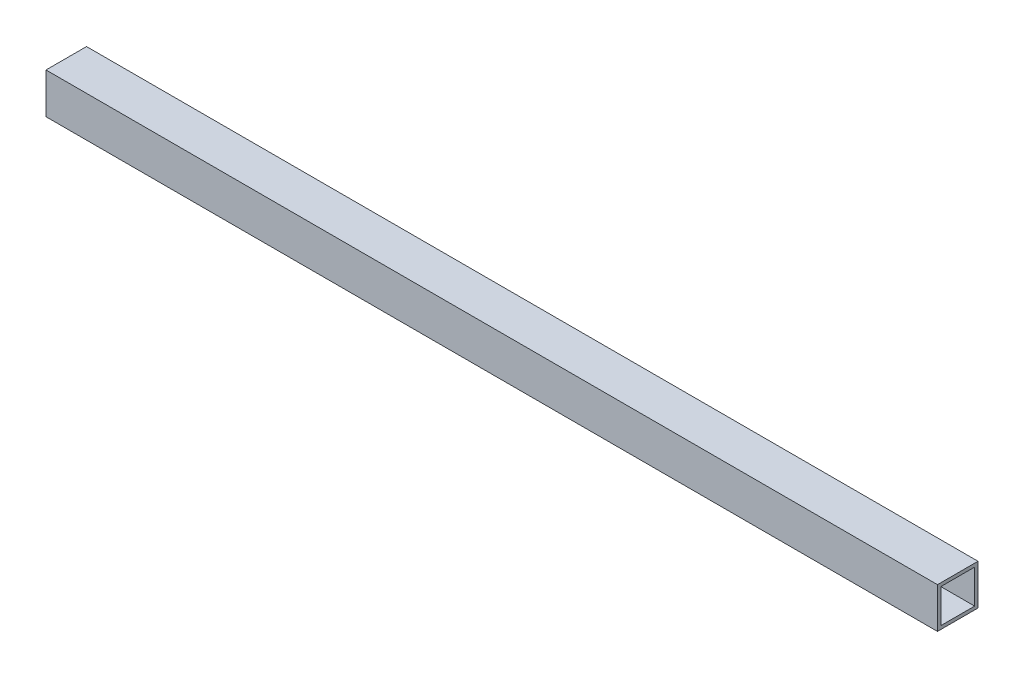
SolidWorks part; units mm, degrees
ref_plane "Front Plane" through (0, 0, 0) normal (0, 0, 1) x (1, 0, 0)
ref_plane "Top Plane" through (0, 0, 0) normal (0, 1, 0) x (1, 0, 0)
ref_plane "Right Plane" through (0, 0, 0) normal (1, 0, 0) x (0, 0, -1)
sketch "Sketch1" plane through (0, 0, 0) normal (0, 0, 1) x (1, 0, 0)
  line L1 (0, 0) -> (838.1, 0)
  line L2 (0, 0) -> (0, 38.1)
  line L3 (0, 38.1) -> (838.1, 38.1)
  line L4 (838.1, 0) -> (838.1, 38.1)
  dimension "D1" = 838.1
  dimension "D2" = 38.1
extrude "Boss-Extrude1" add sketch "Sketch1" against normal blind 38.1
sketch "Sketch2" plane through (838.1, 0, 0) normal (1, 0, 0) x (0, 0, -1)
  line L1 (38.1, 38.1) -> (0, 38.1) construction
  line L2 (38.1, 38.1) -> (38.1, 0) construction
  line L3 (38.1, 0) -> (0, 0) construction
  line L4 (0, 38.1) -> (0, 0) construction
  line L5 (34.925, 3.175) -> (3.175, 3.175)
  line L6 (34.925, 3.175) -> (34.925, 34.925)
  line L7 (34.925, 34.925) -> (3.175, 34.925)
  line L8 (3.175, 3.175) -> (3.175, 34.925)
  line L9 (34.925, 3.175) -> (3.175, 34.925) construction
  line L10 (34.925, 34.925) -> (3.175, 3.175) construction
  point P6 (0, 19.05)
  point P7 (19.05, 38.1)
  point P8 (19.05, 19.05)
  point P11 (19.05, 19.05)
  dimension "D1" = 3.175
extrude "Cut-Extrude1" cut sketch "Sketch2" against normal through all both and the other way through all contours L6 L5 L8 L7
